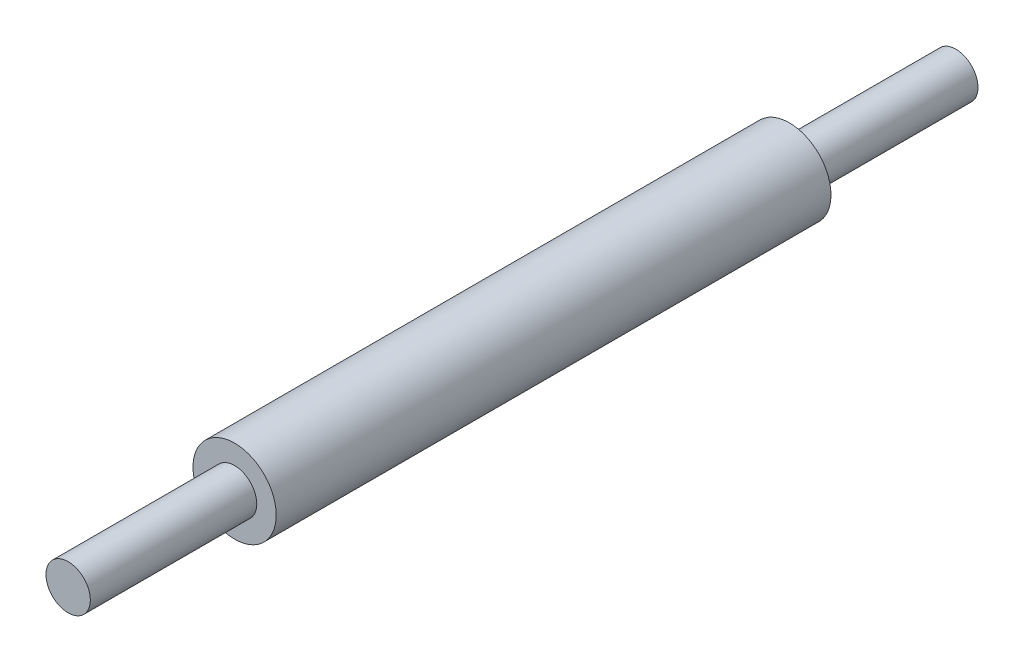
SolidWorks part; units mm, degrees
ref_plane "Front Plane" through (0, 0, 0) normal (0, 0, 1) x (1, 0, 0)
ref_plane "Top Plane" through (0, 0, 0) normal (0, 1, 0) x (1, 0, 0)
ref_plane "Right Plane" through (0, 0, 0) normal (1, 0, 0) x (0, 0, -1)
sketch "Sketch1" plane through (0, 0, 0) normal (0, 0, 1) x (1, 0, 0)
  circle A0 centre (0, 0) radius 0.75
  dimension "D1" = 1.5
extrude "Boss-Extrude1" add sketch "Sketch1" along normal blind 10
sketch "Sketch3" plane through (0, 0, 10) normal (0, 0, 1) x (1, 0, 0)
  circle A0 centre (0, 0) radius 0.4
  dimension "D1" = 0.8
extrude "Boss-Extrude2" add sketch "Sketch3" along normal blind 3
sketch "Sketch4" plane through (0, 0, 0) normal (0, 0, -1) x (-1, 0, 0)
  circle A0 centre (0, 0) radius 0.4
  dimension "D1" = 0.8
extrude "Boss-Extrude3" add sketch "Sketch4" along normal blind 3
